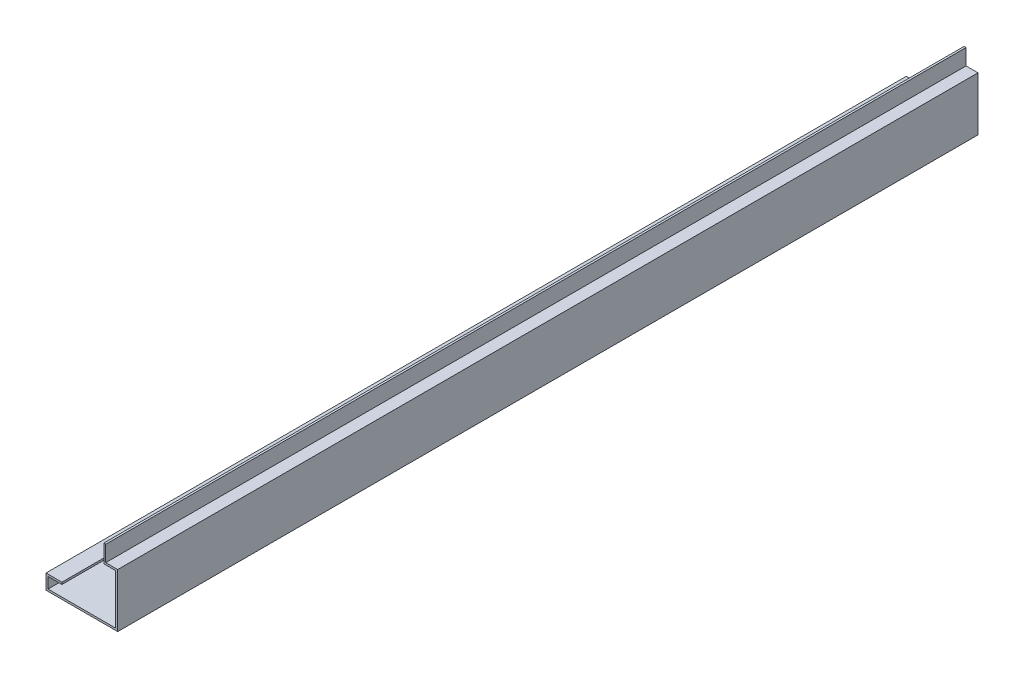
SolidWorks part; units mm, degrees
ref_plane "Alzado" through (0, 0, 0) normal (0, 0, 1) x (1, 0, 0)
ref_plane "Planta" through (0, 0, 0) normal (0, 1, 0) x (1, 0, 0)
ref_plane "Vista lateral" through (0, 0, 0) normal (1, 0, 0) x (0, 0, -1)
sketch "Croquis1" plane through (0, 0, 0) normal (0, 0, 1) x (1, 0, 0)
  line L0 (-139.7, -174.625) -> (-139.7, -180.975)
  line L1 (0, 0) -> (0, -50.8)
  line L2 (0, -50.8) -> (38.1, -50.8)
  line L3 (38.1, -50.8) -> (38.1, -222.25)
  line L4 (38.1, -222.25) -> (-190.5, -222.25)
  line L5 (-190.5, -222.25) -> (-190.5, -174.625)
  line L6 (-190.5, -174.625) -> (-139.7, -174.625)
  line L7 (-139.7, -180.975) -> (-184.15, -180.975)
  line L8 (-184.15, -180.975) -> (-184.15, -215.9)
  line L9 (-184.15, -215.9) -> (31.75, -215.9)
  line L10 (31.75, -215.9) -> (31.75, -57.15)
  line L11 (31.75, -57.15) -> (-6.35, -57.15)
  line L12 (-6.35, -57.15) -> (-6.35, 0)
  line L13 (-6.35, 0) -> (0, 0)
  dimension "D2" = 38.1
  dimension "D3" = 171.45
  dimension "D4" = 228.6
  dimension "D5" = 47.625
  dimension "D6" = 50.8
  dimension "D7" = 6.35
  dimension "D8" = 6.35
  dimension "D9" = 6.35
  dimension "D10" = 6.35
  dimension "D11" = 6.35
  dimension "D12" = 6.35
  dimension "D13" = 57.15
extrude "Saliente-Extruir1" add sketch "Croquis1" against normal blind 2743.2
